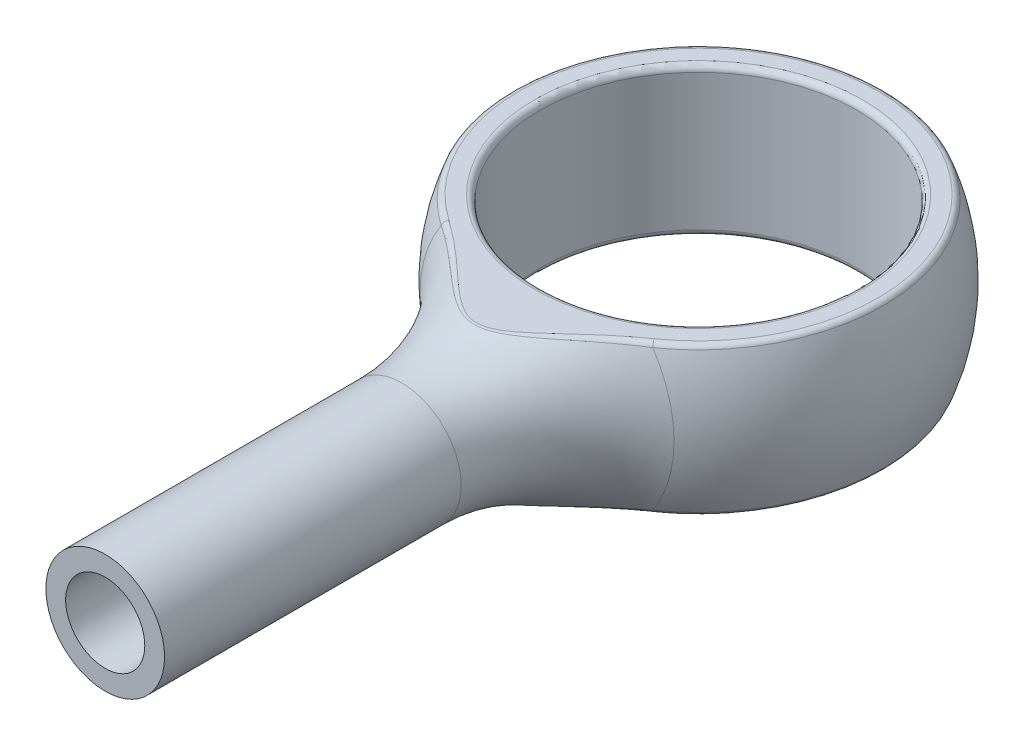
SolidWorks part; units mm, degrees
material "Aleación 1060"
ref_plane "Front Plane" through (0, 0, 0) normal (0, 0, 1) x (1, 0, 0)
ref_plane "Top Plane" through (0, 0, 0) normal (0, 1, 0) x (1, 0, 0)
ref_plane "Right Plane" through (0, 0, 0) normal (1, 0, 0) x (0, 0, -1)
sketch "Sketch1" plane through (0, 0, 0) normal (0, 1, 0) x (1, 0, 0)
  line L0 (-1.5, -15) -> (1.5, -15)
  line L1 (-1.5, -15) -> (-1.5, -7.5)
  line L2 (0, 0) -> (0, -6.9854) construction
  line L3 (1.5, -15) -> (1.5, -7.5)
  circle A0 centre (0, 0) radius 2
  circle A1 centre (0, 0) radius 4
  circle A2 centre (0, 0) radius 5
  arc A3 (-3.2117, -3.8321) -> (-1.5, -7.5) centre (-6.2857, -7.5) cw
  arc A4 (3.2117, -3.8321) -> (1.5, -7.5) centre (6.2857, -7.5) ccw
  point P8 (0, -15)
  dimension "D1" = 10
  dimension "D2" = 8
  dimension "D3" = 4
  dimension "D4" = 15
  dimension "D5" = 3
  dimension "D6" = 7.5
sketch "Sketch2" plane through (0, 0, 0) normal (0, 1, 0) x (1, 0, 0)
  line L0 (-1.5, -15) -> (-1.5, -7.5) construction
  line L1 (-1.5, -15) -> (-1.5, -7.5)
  line L2 (0, 0) -> (0, 7.9404) construction
  line L3 (-1.5, -15) -> (0, -15)
  line L4 (0, 5) -> (0, -15)
  arc A0 (-1.5, -7.5) -> (-3.2117, -3.8321) centre (-6.2857, -7.5) ccw construction
  arc A1 (-1.5, -7.5) -> (-3.2117, -3.8321) centre (-6.2857, -7.5) ccw
  circle A2 centre (0, 0) radius 5 construction
  arc A3 (0, 5) -> (-3.2117, -3.8321) centre (0, 0) ccw
revolve "Revolve1" add sketch "Sketch2" angle 360 about L2
sketch "Sketch4" plane through (0, 0, 0) normal (1, 0, 0) x (0, 0, -1)
  line L0 (0, 0) -> (12.2381, 0) construction
  line L1 (8.7815, 1.875) -> (-9.2674, 1.875)
  line L2 (-12.1353, 2.7792) -> (-18.9876, 7.5772)
  line L3 (-18.9876, 7.5772) -> (8.7815, 7.5772)
  line L4 (8.7815, 7.5772) -> (8.7815, 1.875)
  line L5 (8.7815, -7.5772) -> (8.7815, -1.875)
  line L6 (-18.9876, -7.5772) -> (8.7815, -7.5772)
  line L7 (-12.1353, -2.7792) -> (-18.9876, -7.5772)
  line L8 (8.7815, -1.875) -> (-9.2674, -1.875)
  arc A0 (-9.2674, 1.875) -> (-12.1353, 2.7792) centre (-9.2674, 6.875) cw
  arc A1 (-9.2674, -1.875) -> (-12.1353, -2.7792) centre (-9.2674, -6.875) ccw
  dimension "D3" = 5
  dimension "D1" = 1.875
  dimension "D2" = 145
extrude "Cut-Extrude1" cut sketch "Sketch4" against normal through all both and the other way through all
sketch "Sketch5" plane through (0, 0, 0) normal (0, 1, 0) x (1, 0, 0)
  circle A0 centre (0, 0) radius 4 construction
  circle A1 centre (0, 0) radius 4
extrude "Cut-Extrude2" cut sketch "Sketch5" against normal through all both and the other way through all
fillet "Fillet1" radius 0.15 6 edges at (-0.1513, -1.875, 5.6285) (0, -1.875, -4.6351) (0.1513, 1.875, 5.6285) (0, 1.875, -4.6351) (0, 1.875, 4) (0, -1.875, 4)
sketch "Sketch6" plane through (0, 0, 15) normal (0, 0, 1) x (1, 0, 0)
  circle A0 centre (0, 0) radius 1
  dimension "D1" = 2
extrude "Cut-Extrude3" cut sketch "Sketch6" against normal blind 5
